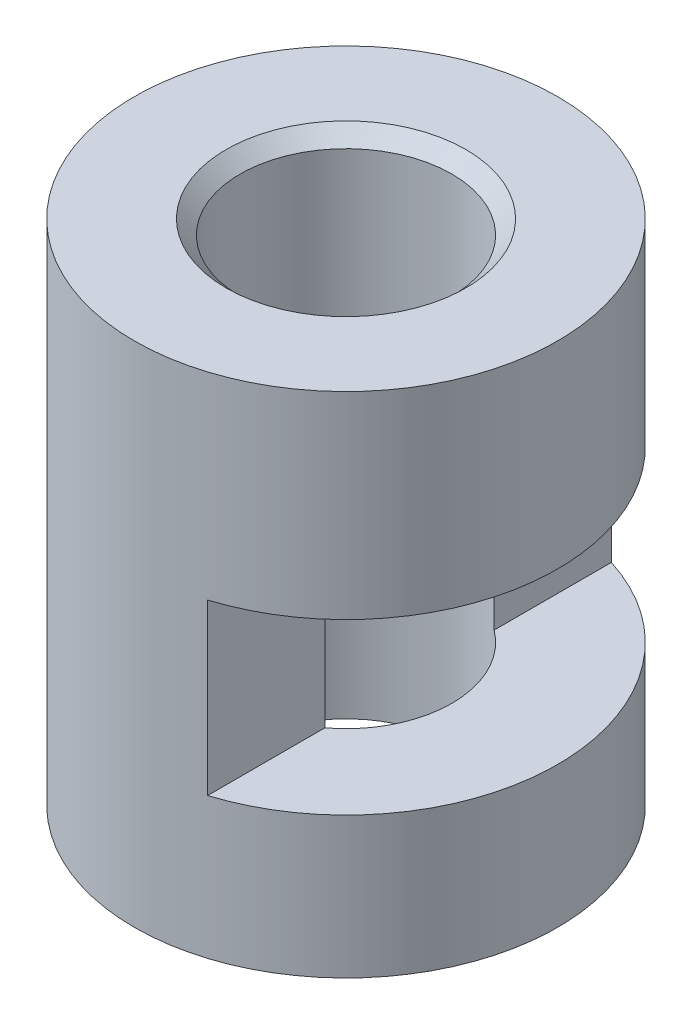
SolidWorks part; units mm, degrees
ref_plane "Front Plane" through (0, 0, 0) normal (0, 0, 1) x (1, 0, 0)
ref_plane "Top Plane" through (0, 0, 0) normal (0, 1, 0) x (1, 0, 0)
ref_plane "Right Plane" through (0, 0, 0) normal (1, 0, 0) x (0, 0, -1)
sketch "Sketch1" plane through (0, 0, 0) normal (0, 1, 0) x (1, 0, 0)
  circle A0 centre (0, 0) radius 3
  dimension "D1" = 6
extrude "Boss-Extrude1" add sketch "Sketch1" along normal blind 7.2
sketch "Sketch2" plane through (0, 7.2, 0) normal (0, 1, 0) x (1, 0, 0)
  circle A0 centre (0, 0) radius 1.5
  dimension "D1" = 3
extrude "Cut-Extrude1" cut sketch "Sketch2" against normal up to next
sketch "Sketch3" plane through (0, 0, 0) normal (0, 0, 1) x (1, 0, 0)
  line L0 (3, 7.2) -> (-3, 7.2) construction
  line L1 (0.9, 4.4) -> (3, 4.4)
  line L2 (0.9, 4.4) -> (0.9, 2)
  line L3 (0.9, 2) -> (3, 2)
  line L5 (-1.5, 7.2) -> (-1.5, 0) construction
  line L6 (3, 0) -> (3, 7.2) construction
  line L7 (3, 2) -> (3, 4.4)
  dimension "D1" = 2.4
  dimension "D2" = 2.8
  dimension "D3" = 2.4
extrude "Cut-Extrude2" cut sketch "Sketch3" against normal through all both and the other way through all
chamfer "Chamfer1" distance 0.2 angle 45 1 edges at (0, 7.2, 1.5)
